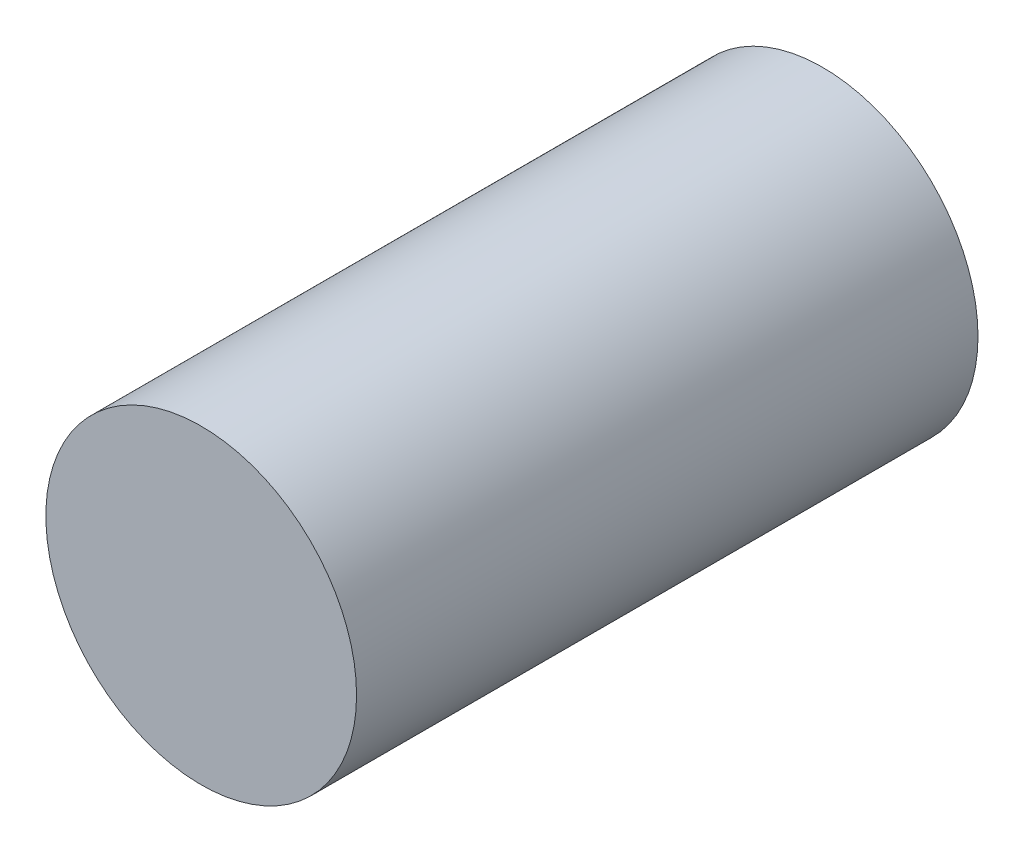
SolidWorks part; units mm, degrees
ref_plane "Plan de face" through (0, 0, 0) normal (0, 0, 1) x (1, 0, 0)
ref_plane "Plan de dessus" through (0, 0, 0) normal (0, 1, 0) x (1, 0, 0)
ref_plane "Plan de droite" through (0, 0, 0) normal (1, 0, 0) x (0, 0, -1)
sketch "Esquisse1" plane through (0, 0, 0) normal (0, 0, 1) x (1, 0, 0)
  circle A0 centre (0, 0) radius 20
  dimension "D1" = 40
extrude "Boss.-Extru.1" add sketch "Esquisse1" along normal blind 80
